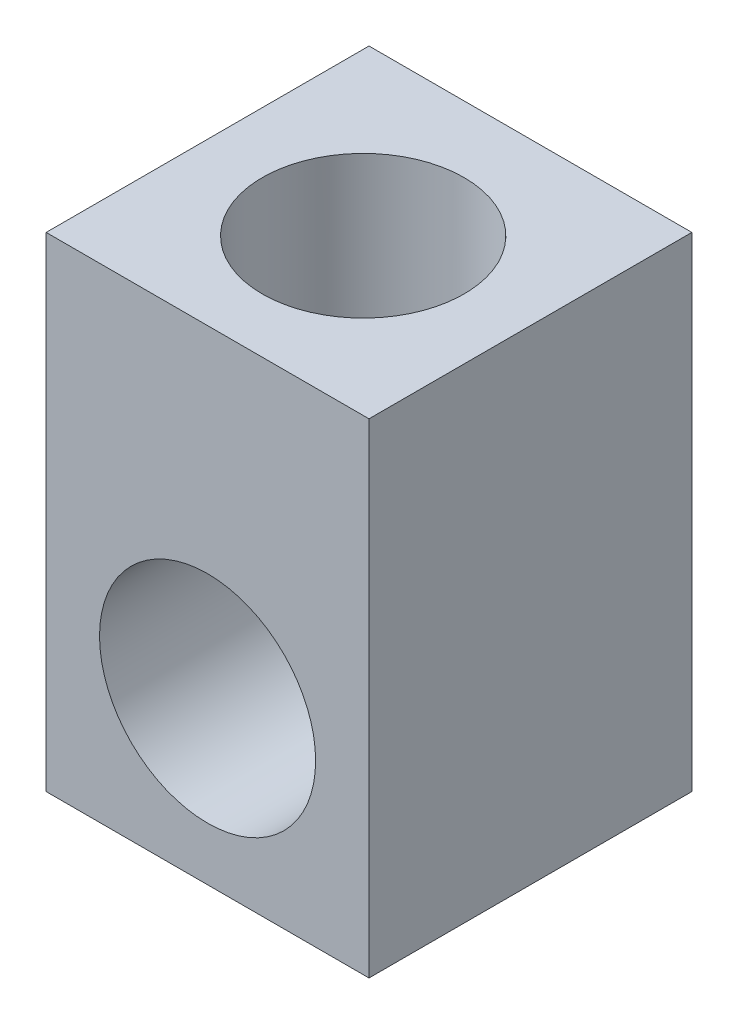
SolidWorks part; units mm, degrees
ref_plane "Front Plane" through (0, 0, 0) normal (0, 0, 1) x (1, 0, 0)
ref_plane "Top Plane" through (0, 0, 0) normal (0, 1, 0) x (1, 0, 0)
ref_plane "Right Plane" through (0, 0, 0) normal (1, 0, 0) x (0, 0, -1)
sketch "Sketch1" plane through (0, 0, 0) normal (0, 1, 0) x (1, 0, 0)
  line L1 (0, 0) -> (50.8, 0)
  line L2 (0, 0) -> (0, 50.8)
  line L3 (0, 50.8) -> (50.8, 50.8)
  line L4 (50.8, 0) -> (50.8, 50.8)
  dimension "D1" = 50.8
  dimension "D2" = 50.8
extrude "Boss-Extrude1" add sketch "Sketch1" along normal blind 76.2
sketch "Sketch2" plane through (0, 0, -50.8) normal (0, 0, -1) x (-1, 0, 0)
  line L1 (0, 0) -> (-25.4, 0)
  line L2 (0, 0) -> (0, 25.4)
  line L3 (0, 25.4) -> (-25.4, 25.4)
  line L4 (-25.4, 0) -> (-25.4, 25.4)
  circle A0 centre (-25.4, 25.4) radius 17
  dimension "D1" = 25.4
  dimension "D2" = 25.4
extrude "Cut-Extrude1" cut sketch "Sketch2" against normal blind 76.2 contours L3 A0 L4 | L4 A0 L3
sketch "Sketch3" plane through (0, 76.2, 0) normal (0, 1, 0) x (1, 0, 0)
  line L1 (0, 50.8) -> (25.4, 50.8)
  line L2 (0, 50.8) -> (0, 24.4856)
  line L3 (0, 24.4856) -> (25.4, 24.4856)
  line L4 (25.4, 50.8) -> (25.4, 24.4856)
  circle A0 centre (25.4, 24.4856) radius 15.875
extrude "Cut-Extrude2" cut sketch "Sketch3" against normal up to next contours L3 A0 L4 | L4 A0 L3
